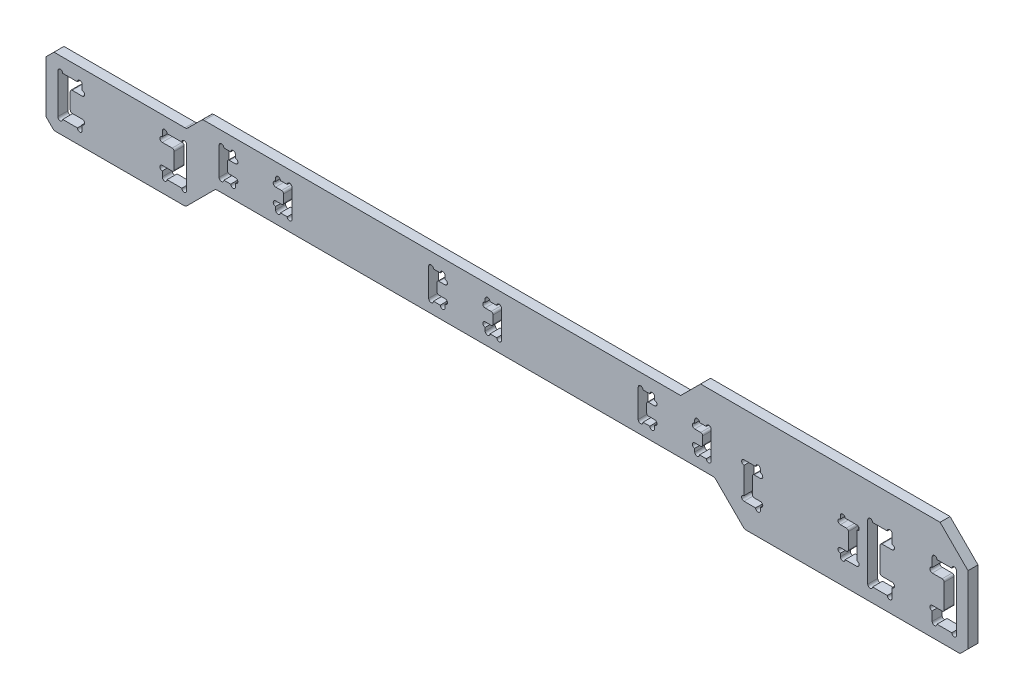
SolidWorks part; units mm, degrees
ref_plane "前视基准面" through (0, 0, 0) normal (0, 0, 1) x (1, 0, 0)
ref_plane "上视基准面" through (0, 0, 0) normal (0, 1, 0) x (1, 0, 0)
ref_plane "右视基准面" through (0, 0, 0) normal (1, 0, 0) x (0, 0, -1)
sketch "草图1" plane through (0, 0, 0) normal (0, 0, 1) x (1, 0, 0)
  line L0 (-106.425, 2.5) -> (-109.425, 2.5)
  line L1 (115.5, -8.5) -> (-115.5, -8.5)
  line L2 (115.5, -8.5) -> (115.5, 8.5)
  line L3 (115.5, 8.5) -> (-115.5, 8.5)
  line L4 (-115.5, -8.5) -> (-115.5, 8.5)
  line L5 (115.5, -8.5) -> (-115.5, 8.5) construction
  line L6 (115.5, 8.5) -> (-115.5, -8.5) construction
  line L7 (-106.425, -5) -> (-112.525, -5)
  line L8 (-106.425, -5) -> (-106.425, -2.5)
  line L9 (-106.425, 5) -> (-112.525, 5)
  line L10 (-112.525, -5) -> (-112.525, 5)
  line L11 (-106.425, -5) -> (-112.525, 5) construction
  line L12 (-106.425, 5) -> (-112.525, -5) construction
  line L13 (-80.275, -5) -> (-86.375, -5)
  line L14 (-80.275, -5) -> (-80.275, 5)
  line L15 (-80.275, 5) -> (-86.375, 5)
  line L16 (-86.375, -5) -> (-86.375, -2.5)
  line L17 (-80.275, -5) -> (-86.375, 5) construction
  line L18 (-80.275, 5) -> (-86.375, -5) construction
  line L19 (-109.425, 2.5) -> (-109.425, -2.5)
  line L20 (-109.425, -2.5) -> (-106.425, -2.5)
  line L21 (-106.425, 2.5) -> (-106.425, 5)
  line L22 (-86.375, 2.5) -> (-83.375, 2.5)
  line L23 (-83.375, 2.5) -> (-83.375, -2.5)
  line L24 (-83.375, -2.5) -> (-86.375, -2.5)
  line L25 (-86.375, 2.5) -> (-86.375, 5)
  line L26 (-109.475, 0) -> (-83.325, 0) construction
  point P0 (0, 0)
  point P5 (-109.475, 0)
  point P11 (-83.325, 0)
  point P26 (-96.4, 0)
  dimension "D1" = 17
  dimension "D2" = 231
  dimension "D3" = 10
  dimension "D4" = 19.1
  dimension "D5" = 3.1
  dimension "D6" = 3
  dimension "D7" = 5
  dimension "D8" = 20.05
extrude "凸台-拉伸1" add sketch "草图1" along normal mid plane 2.5
sketch "草图2" plane through (0, 0, 1.25) normal (0, 0, 1) x (1, 0, 0)
  line L0 (-106.425, 2.5) -> (-106.425, 5) construction
  line L1 (-106.425, -5) -> (-106.425, -2.5) construction
  line L2 (-106.425, 5) -> (-112.525, 5) construction
  line L3 (-112.525, -5) -> (-106.425, -5) construction
  line L5 (-86.375, 5) -> (-86.375, 2.5) construction
  line L6 (-86.375, -2.5) -> (-86.375, -5) construction
  line L7 (-80.275, 5) -> (-86.375, 5) construction
  line L8 (-86.375, -5) -> (-80.275, -5) construction
  circle A0 centre (-106.425, 3.1) radius 0.6
  circle A1 centre (-106.425, -3.1) radius 0.6
  circle A2 centre (-107.025, 5) radius 0.6
  circle A3 centre (-107.025, -5) radius 0.6
  circle A5 centre (-111.925, -5) radius 0.6
  circle A6 centre (-111.925, 5) radius 0.6
  circle A7 centre (-86.375, 3.1) radius 0.6
  circle A8 centre (-86.375, -3.1) radius 0.6
  circle A9 centre (-85.775, 5) radius 0.6
  circle A10 centre (-80.875, 5) radius 0.6
  circle A11 centre (-85.775, -5) radius 0.6
  circle A12 centre (-80.875, -5) radius 0.6
  dimension "D1" = 1.2
extrude "切除-拉伸1" cut sketch "草图2" against normal through all
fillet "圆角1" radius 0.5 4 edges at (-83.375, -2.5, 0) (-83.375, 2.5, 0) (-109.425, -2.5, 0) (-109.425, 2.5, 0)
chamfer "倒角1" distance 2 angle 45 2 edges at (-115.5, -8.5, 0) (-115.5, 8.5, 0)
sketch "草图3" plane through (0, 0, 1.25) normal (0, 0, 1) x (1, 0, 0)
  line L0 (-115.5, 6.5) -> (-115.5, -6.5) construction
  line L1 (-113.5, -8.5) -> (115.5, -8.5) construction
  line L2 (-73, -1) -> (52, -1)
  line L3 (52, -1) -> (59.5, -8.5)
  line L5 (-73, -1) -> (-80.5, -8.5)
  line L6 (-80.5, -8.5) -> (59.5, -8.5)
  dimension "D1" = 42.5
  dimension "D2" = 140
  dimension "D3" = 7.5
  dimension "D4" = 45
extrude "切除-拉伸2" cut sketch "草图3" against normal through all
sketch "草图4" plane through (0, 0, 1.25) normal (0, 0, 1) x (1, 0, 0)
  line L0 (-80.275, 8.5) -> (-76.275, 12.5)
  line L1 (115.5, 8.5) -> (-113.5, 8.5) construction
  line L2 (-80.275, -5) -> (-80.275, 5) construction
  line L3 (-76.275, 12.5) -> (115.5, 12.5)
  line L4 (115.5, 12.5) -> (115.5, 8.5)
  line L5 (115.5, 8.5) -> (-80.275, 8.5)
  line L6 (115.5, -8.5) -> (115.5, 8.5) construction
  line L7 (-73, -1) -> (-80.5, -8.5) construction
  dimension "D1" = 4
extrude "凸台-拉伸2" add sketch "草图4" against normal blind 2.5
sketch "草图5" plane through (0, 0, 1.25) normal (0, 0, 1) x (1, 0, 0)
  line L0 (-68.025, 9) -> (-72.125, 9)
  line L1 (-72.125, 9) -> (-72.125, 2)
  line L2 (-72.125, 2) -> (-68.025, 2)
  line L3 (-68.025, 2) -> (-68.025, 4)
  line L4 (-68.025, 4) -> (-70.025, 4)
  line L5 (-70.025, 4) -> (-70.025, 7)
  line L6 (-70.025, 7) -> (-68.025, 7)
  line L7 (-68.025, 7) -> (-68.025, 9)
  line L8 (-57.975, 9) -> (-57.975, 7)
  line L9 (-57.975, 7) -> (-55.975, 7)
  line L10 (-55.975, 7) -> (-55.975, 4)
  line L11 (-55.975, 4) -> (-57.975, 4)
  line L12 (-57.975, 4) -> (-57.975, 2)
  line L13 (-57.975, 2) -> (-53.875, 2)
  line L14 (-53.875, 2) -> (-53.875, 9)
  line L15 (-53.875, 9) -> (-57.975, 9)
  line L16 (-70.025, 5.5) -> (-55.975, 5.5) construction
  line L17 (115.5, 12.5) -> (-76.275, 12.5) construction
  line L19 (-63, 9) -> (-63, 2) construction
  line L20 (-115.5, 6.5) -> (-115.5, -6.5) construction
  point P21 (-63, 5.5)
  dimension "D1" = 7
  dimension "D2" = 52.5
  dimension "D3" = 3
  dimension "D4" = 10.05
  dimension "D5" = 2
  dimension "D6" = 2.1
  dimension "D7" = 2
extrude "切除-拉伸3" cut sketch "草图5" against normal through all and the other way through all
sketch "草图6" plane through (0, 0, 1.25) normal (0, 0, 1) x (1, 0, 0)
  line L0 (-68.025, 7) -> (-68.025, 9) construction
  line L1 (-68.025, 9) -> (-72.125, 9) construction
  line L2 (-72.125, 2) -> (-68.025, 2) construction
  line L3 (-68.025, 2) -> (-68.025, 4) construction
  line L4 (-57.975, 4) -> (-57.975, 2) construction
  line L5 (-57.975, 9) -> (-57.975, 7) construction
  line L6 (-53.875, 9) -> (-57.975, 9) construction
  line L7 (-57.975, 2) -> (-53.875, 2) construction
  circle A0 centre (-68.025, 7.6) radius 0.6
  circle A1 centre (-68.625, 9) radius 0.6
  circle A2 centre (-71.525, 9) radius 0.6
  circle A3 centre (-71.525, 2) radius 0.6
  circle A4 centre (-68.025, 3.4) radius 0.6
  circle A5 centre (-68.625, 2) radius 0.6
  circle A6 centre (-57.975, 3.4) radius 0.6
  circle A7 centre (-57.975, 7.6) radius 0.6
  circle A8 centre (-57.375, 9) radius 0.6
  circle A9 centre (-57.375, 2) radius 0.6
  circle A10 centre (-54.475, 2) radius 0.6
  circle A11 centre (-54.475, 9) radius 0.6
  dimension "D1" = 1.2
extrude "切除-拉伸4" cut sketch "草图6" against normal through all
fillet "圆角2" radius 0.5 4 edges at (-55.975, 4, 0) (-55.975, 7, 0) (-70.025, 7, 0) (-70.025, 4, 0)
pattern_linear "阵列(线性)1" count 3 spacing 52.5 along (1, 0, 0) of "切除-拉伸4", "切除-拉伸3", "圆角2"
sketch "草图7" plane through (0, 0, 1.25) normal (0, 0, 1) x (1, 0, 0)
  line L0 (106.525, 9) -> (112.625, 9)
  line L1 (112.625, 9) -> (112.625, -5)
  line L2 (112.625, -5) -> (106.525, -5)
  line L3 (106.525, -5) -> (106.525, -1.5)
  line L4 (106.525, -1.5) -> (109.525, -1.5)
  line L5 (109.525, -1.5) -> (109.525, 5.5)
  line L6 (109.525, 5.5) -> (106.525, 5.5)
  line L7 (106.525, 5.5) -> (106.525, 9)
  line L8 (101.5, 9) -> (101.5, -5) construction
  line L9 (115.5, -8.5) -> (115.5, 12.5) construction
  line L10 (112.625, 2) -> (115.5, 2) construction
  line L11 (96.475, 5.5) -> (96.475, 9)
  line L12 (93.475, 5.5) -> (96.475, 5.5)
  line L13 (93.475, -1.5) -> (93.475, 5.5)
  line L14 (96.475, -1.5) -> (93.475, -1.5)
  line L15 (96.475, -5) -> (96.475, -1.5)
  line L16 (90.375, -5) -> (96.475, -5)
  line L17 (90.375, 9) -> (90.375, -5)
  line L18 (96.475, 9) -> (90.375, 9)
  dimension "D1" = 10.05
  dimension "D2" = 3
  dimension "D3" = 3.1
  dimension "D4" = 14
  dimension "D5" = 14
  dimension "D6" = 7
extrude "切除-拉伸5" cut sketch "草图7" against normal through all
sketch "草图8" plane through (0, 0, 1.25) normal (0, 0, 1) x (1, 0, 0)
  line L0 (96.475, 9) -> (90.375, 9) construction
  line L1 (96.475, 5.5) -> (96.475, 9) construction
  line L2 (96.475, -5) -> (96.475, -1.5) construction
  line L3 (90.375, -5) -> (96.475, -5) construction
  line L4 (106.525, 9) -> (106.525, 5.5) construction
  line L5 (106.525, -1.5) -> (106.525, -5) construction
  line L6 (112.625, 9) -> (106.525, 9) construction
  line L7 (106.525, -5) -> (112.625, -5) construction
  circle A0 centre (90.975, 9) radius 0.6
  circle A1 centre (95.875, 9) radius 0.6
  circle A2 centre (96.475, 6.1) radius 0.6
  circle A3 centre (96.475, -2.1) radius 0.6
  circle A4 centre (95.875, -5) radius 0.6
  circle A5 centre (90.975, -5) radius 0.6
  circle A6 centre (106.525, 6.1) radius 0.6
  circle A7 centre (106.525, -2.1) radius 0.6
  circle A8 centre (107.125, 9) radius 0.6
  circle A9 centre (112.025, 9) radius 0.6
  circle A10 centre (112.025, -5) radius 0.6
  circle A11 centre (107.125, -5) radius 0.6
  dimension "D1" = 1.2
extrude "切除-拉伸6" cut sketch "草图8" against normal through all
fillet "圆角3" radius 0.5 4 edges at (109.525, -1.5, 0) (109.525, 5.5, 0) (93.475, -1.5, 0) (93.475, 5.5, 0)
fillet "圆角4" radius 1 6 edges at (-76.275, 12.5, 0) (-80.275, 8.5, 0) (59.5, -8.5, 0) (52, -1, 0) (-73, -1, 0) (-80.5, -8.5, 0)
chamfer "倒角2" distance 2 angle 45 2 edges at (115.5, 12.5, 0) (115.5, -8.5, 0)
sketch "草图9" plane through (0, 0, 1.25) normal (0, 0, 1) x (1, 0, 0)
  line L0 (113.5, 12.5) -> (108.5, 17.5)
  line L1 (108.5, 17.5) -> (48.5, 17.5)
  line L2 (48.5, 17.5) -> (43.5, 12.5)
  line L3 (113.5, 12.5) -> (-75.8608, 12.5) construction
  line L4 (43.5, 12.5) -> (113.5, 12.5)
  line L5 (115.5, 10.5) -> (113.5, 12.5) construction
  dimension "D1" = 5
  dimension "D2" = 70
extrude "凸台-拉伸3" add sketch "草图9" against normal up to surface (2.5 mm away)
sketch "草图10" plane through (0, 0, 1.25) normal (0, 0, 1) x (1, 0, 0)
  line L0 (59.375, 6.5) -> (63.475, 6.5)
  line L1 (63.475, 6.5) -> (63.475, 4.5)
  line L2 (63.475, 4.5) -> (61.475, 4.5)
  line L3 (61.475, 4.5) -> (61.475, -0.5)
  line L4 (61.475, -0.5) -> (63.475, -0.5)
  line L5 (63.475, -0.5) -> (63.475, -2.5)
  line L6 (63.475, -2.5) -> (59.375, -2.5)
  line L7 (59.375, -2.5) -> (59.375, 6.5)
  line L8 (83.525, 6.5) -> (83.525, 4.5)
  line L9 (85.525, 4.5) -> (85.525, -0.5)
  line L10 (85.525, -0.5) -> (83.525, -0.5)
  line L11 (83.525, -0.5) -> (83.525, -2.5)
  line L12 (83.525, -2.5) -> (87.625, -2.5)
  line L13 (87.625, -2.5) -> (87.625, 6.5)
  line L14 (87.625, 6.5) -> (83.525, 6.5)
  line L15 (83.525, 4.5) -> (85.525, 4.5)
  line L16 (59.9142, -8.5) -> (113.5, -8.5) construction
  line L18 (63.475, 6.5) -> (83.525, 6.5) construction
  line L19 (73.5, 6.5) -> (73.5, -2.5) construction
  line L21 (115.5, -6.5) -> (115.5, 10.5) construction
  point P20 (0, 0)
  dimension "D1" = 5
  dimension "D2" = 9
  dimension "D3" = 2
  dimension "D4" = 2.1
  dimension "D5" = 6
  dimension "D6" = 20.05
  dimension "D7" = 42
extrude "切除-拉伸7" cut sketch "草图10" against normal through all
sketch "草图11" plane through (0, 0, 1.25) normal (0, 0, 1) x (1, 0, 0)
  line L0 (63.475, 4.5) -> (63.475, 6.5) construction
  line L1 (63.475, 6.5) -> (59.375, 6.5) construction
  line L2 (59.375, 6.5) -> (59.375, -2.5) construction
  line L3 (59.375, -2.5) -> (63.475, -2.5) construction
  line L5 (83.525, -0.5) -> (83.525, -2.5) construction
  line L6 (83.525, -2.5) -> (87.625, -2.5) construction
  line L7 (87.625, -2.5) -> (87.625, 6.5) construction
  line L8 (83.525, 6.5) -> (83.525, 4.5) construction
  line L9 (87.625, 6.5) -> (83.525, 6.5) construction
  line L10 (63.475, -2.5) -> (63.475, -0.5) construction
  circle A0 centre (63.475, 5.1) radius 0.6
  circle A1 centre (62.875, 6.5) radius 0.6
  circle A2 centre (59.375, 5.9) radius 0.6
  circle A3 centre (59.375, -1.9) radius 0.6
  circle A4 centre (63.475, -1.1) radius 0.6
  circle A5 centre (62.875, -2.5) radius 0.6
  circle A6 centre (83.525, -1.1) radius 0.6
  circle A7 centre (84.125, -2.5) radius 0.6
  circle A8 centre (87.625, -1.9) radius 0.6
  circle A9 centre (87.625, 5.9) radius 0.6
  circle A10 centre (83.525, 5.1) radius 0.6
  circle A11 centre (84.125, 6.5) radius 0.6
  point P54 (63.35, -2.1)
  dimension "D1" = 1.2
extrude "切除-拉伸8" cut sketch "草图11" against normal through all
fillet "圆角5" radius 0.5 4 edges at (85.525, -0.5, 0) (85.525, 4.5, 0) (61.475, -0.5, 0) (61.475, 4.5, 0)
